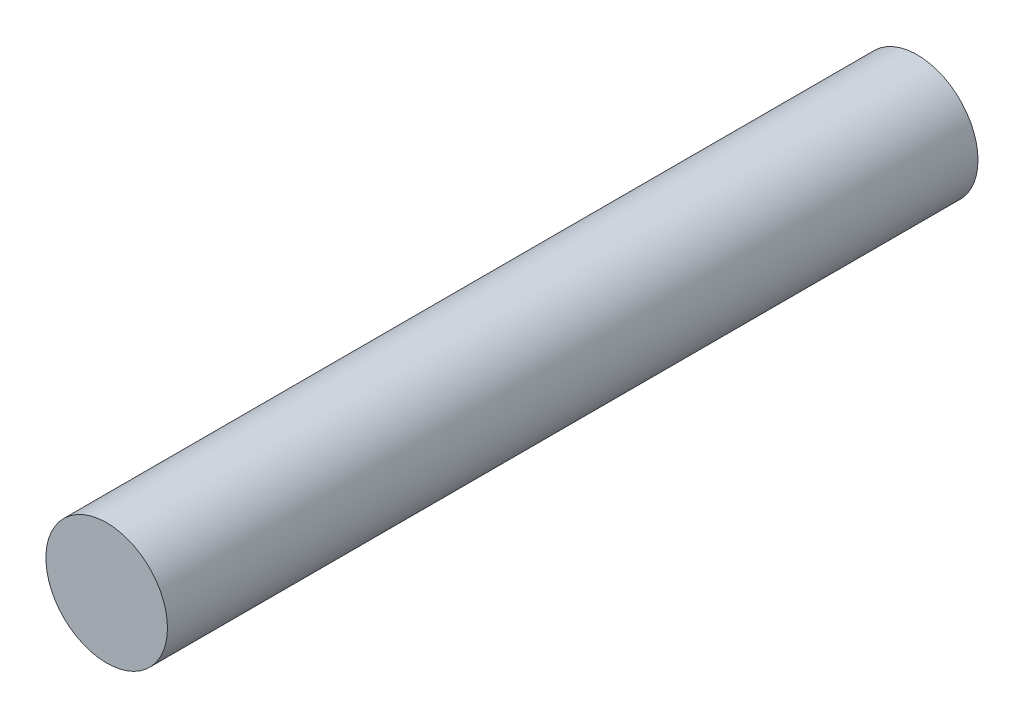
SolidWorks part; units mm, degrees
ref_plane "Front Plane" through (0, 0, 0) normal (0, 0, 1) x (1, 0, 0)
ref_plane "Top Plane" through (0, 0, 0) normal (0, 1, 0) x (1, 0, 0)
ref_plane "Right Plane" through (0, 0, 0) normal (1, 0, 0) x (0, 0, -1)
sketch "Sketch1" plane through (0, 0, 0) normal (0, 0, 1) x (1, 0, 0)
  circle A0 centre (0, 0) radius 1.5
  dimension "D1" = 3
extrude "Boss-Extrude1" add sketch "Sketch1" along normal blind 20 contours A0
